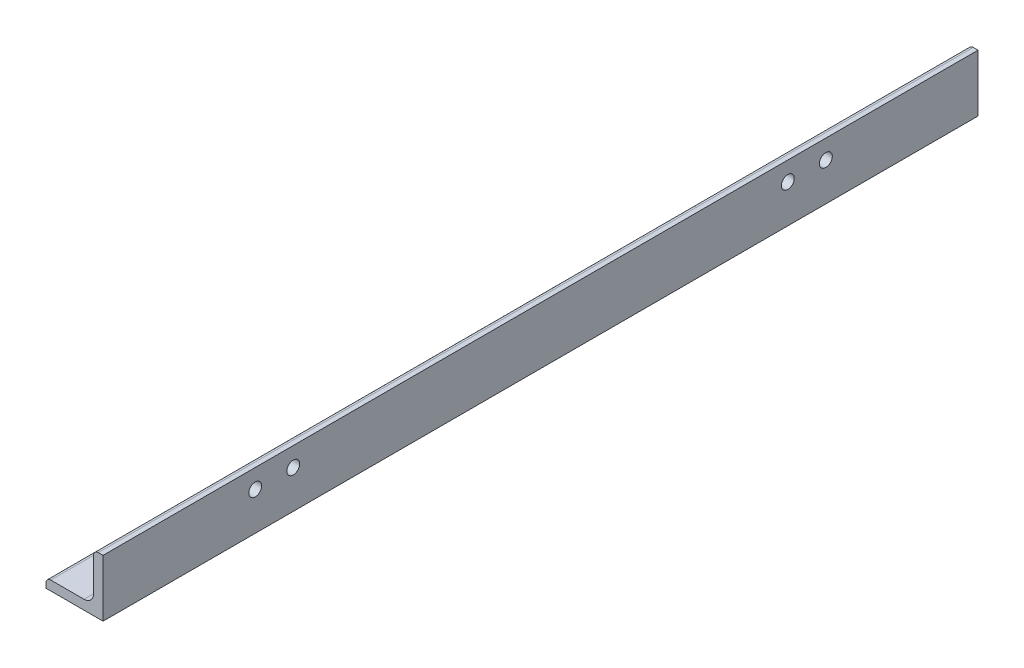
SolidWorks part; units mm, degrees
material "6061-T6 (SS)"
ref_plane "Front Plane" through (0, 0, 0) normal (0, 0, 1) x (1, 0, 0)
ref_plane "Top Plane" through (0, 0, 0) normal (0, 1, 0) x (1, 0, 0)
ref_plane "Right Plane" through (0, 0, 0) normal (1, 0, 0) x (0, 0, -1)
sketch "Sketch0" plane through (0, 0, 0) normal (0, 0, 1) x (1, 0, 0)
  line L0 (-9.525, -9.525) -> (9.525, -9.525)
  line L1 (9.525, -9.525) -> (9.525, 9.525)
  line L2 (9.525, 0) -> (0, 0) construction
  line L3 (0, 0) -> (0, -9.525) construction
  line L4 (6.35, -3.175) -> (6.35, 9.525) construction
  line L5 (3.175, -6.35) -> (-9.525, -6.35) construction
  arc A0 (6.35, -3.175) -> (3.175, -6.35) centre (3.175, -3.175) cw
  point P3 (5.4201, -5.4201)
  dimension "Inside Corner Radius" = 3.175
  dimension "Outside Height" = 19.05
  dimension "Inside Height" = 15.875
  dimension "Inside Width" = 15.875
  dimension "Wall Thickness" = 3.175
  dimension "D1" = 3.175
  dimension "Outside Width" = 19.05
sketch "Sketch1" plane through (0, 0, 0) normal (1, 0, 0) x (0, 0, -1)
  line L0 (146.05, 0) -> (-146.05, 0)
  point P4 (0, 0)
  dimension "Length" = 292.1
sketch "Sketch2" plane through (0, 0, 0) normal (0, 0, 1) x (1, 0, 0)
  line L0 (-9.525, -9.525) -> (9.525, -9.525)
  line L1 (9.525, -9.525) -> (9.525, 9.525)
  line L2 (9.525, 9.525) -> (6.35, 9.525) construction
  line L3 (6.35, 7.9375) -> (6.35, -3.175)
  line L4 (3.175, -6.35) -> (-7.9375, -6.35)
  line L5 (-9.525, -9.525) -> (-9.525, -6.35) construction
  line L6 (7.9375, 9.525) -> (9.525, 9.525)
  line L7 (-9.525, -7.9375) -> (-9.525, -9.525)
  line L8 (9.525, 0) -> (0, 0) construction
  line L9 (0, 0) -> (0, -9.525) construction
  arc A0 (6.35, 7.9375) -> (7.9375, 9.525) centre (7.9375, 7.9375) cw
  arc A1 (-9.525, -7.9375) -> (-7.9375, -6.35) centre (-7.9375, -7.9375) cw
  arc A2 (6.35, -3.175) -> (3.175, -6.35) centre (3.175, -3.175) cw
  dimension "Inside Radius" = 3.175
  dimension "Height" = 19.05
  dimension "Width" = 19.05
  dimension "Thickness" = 3.175
extrude "Boss-Extrude1" add sketch "Sketch2" along normal mid plane 292.1
sketch "Break Locations" plane through (0, 0, 0) normal (1, 0, 0) x (0, 0, -1)
  line L0 (-126.619, 0) -> (126.619, 0)
  line L1 (-146.05, -9.525) -> (-146.05, 9.525) construction
  line L2 (146.05, -9.525) -> (146.05, 9.525) construction
  point P0 (-129.8575, 0)
  point P1 (129.8575, 0)
  point P10 (0, 0)
  point P11 (126.619, 0)
  point P13 (-126.619, 0)
  dimension "D1" = 16.1925
  dimension "D2" = 16.1925
  dimension "D3" = 19.431
ref_plane "Plane1" through (0, 0, 0) normal (0.7071, 0.7071, 0) x (0.7071, -0.7071, 0)
hole_wizard "#18 (0.1695) Diameter Hole1" positions "Sketch16" profile "Sketch17" hole size "#18" standard "ANSI Inch" end condition through all
sketch "Sketch16" plane through (6.35, 0, 0) normal (-1, 0, 0) x (0, 0, 1)
  line L0 (-146.05, 7.9375) -> (-146.05, -3.175) construction
  line L1 (-95.25, 3.175) -> (-82.55, 3.175) construction
  line L3 (-95.25, 3.175) -> (-146.05, 3.175) construction
  line L5 (146.05, -6.35) -> (-146.05, -6.35) construction
  point P0 (-95.25, 3.175)
  point P2 (-82.55, 3.175)
  dimension "D1" = 12.7
  dimension "D2" = 50.8
  dimension "D3" = 9.525
sketch "Sketch17" plane through (6.35, 3.175, -95.25) normal (0, 1, 0) x (0, 0, 1)
  line L0 (0, 0) -> (0, 3.175)
  line L1 (0, 3.175) -> (2.1526, 3.175)
  line L2 (2.1526, 3.175) -> (2.1526, 0)
  line L5 (2.1526, 0) -> (0, 0)
  line L11 (0, -6.35) -> (0, 107.95) construction
  dimension "Thru Hole Dia." = 4.3053
  dimension "Thru Hole Depth" = 3.175
mirror "Mirror1" about plane through (0, 0, 0) normal (0.7071, 0.7071, 0) of "#18 (0.1695) Diameter Hole1"
mirror "Mirror2" about plane through (0, 0, 0) normal (0, 0, 1) of "Mirror1", "#18 (0.1695) Diameter Hole1"
hole_wizard "#8 Clearance Hole1" positions "Sketch18" profile "Sketch19" hole size "#8" standard "ANSI Inch"
sketch "Sketch18" plane through (-14.6065, -6.35, -133.6466) normal (0, 1, 0) x (0, 0, 1)
  point P0 (-1.2909, 16.194)
sketch "Sketch19" plane through (1.5875, -6.35, -134.9375) normal (1, 0, 0) x (0, 0, 1)
  line L0 (0, 0) -> (0, 3.175)
  line L1 (0, 3.175) -> (2.1526, 3.175)
  line L2 (2.1526, 3.175) -> (2.1526, 0)
  line L3 (2.1526, 0) -> (0, 0)
  line L4 (0, -6.35) -> (0, 107.95) construction
  dimension "Thru Hole Dia." = 4.3053
  dimension "Thru Hole Depth" = 3.175
equation "\"D1@Break Locations\" = .85 * \"Height@Sketch2\""
equation "\"D2@Break Locations\"=\"D1@Break Locations\""
equation "\"Thickness@Sketch2\"=\"wall thickness@sketch0\""
equation "\"Height@Sketch2\"=\"outside height@sketch0\""
equation "\"Width@Sketch2\"=\"outside width@sketch0\""
equation "\"Inside Radius@Sketch2\"=\"inside corner radius@sketch0\""
equation "\"Length@Boss-Extrude1\"=\"length@sketch1\""
equation "\"D3@Break Locations\"=\"D2@Break Locations\"*1.2"
equation "\"D1@Sketch0\"=\"Wall Thickness@Sketch0\""
